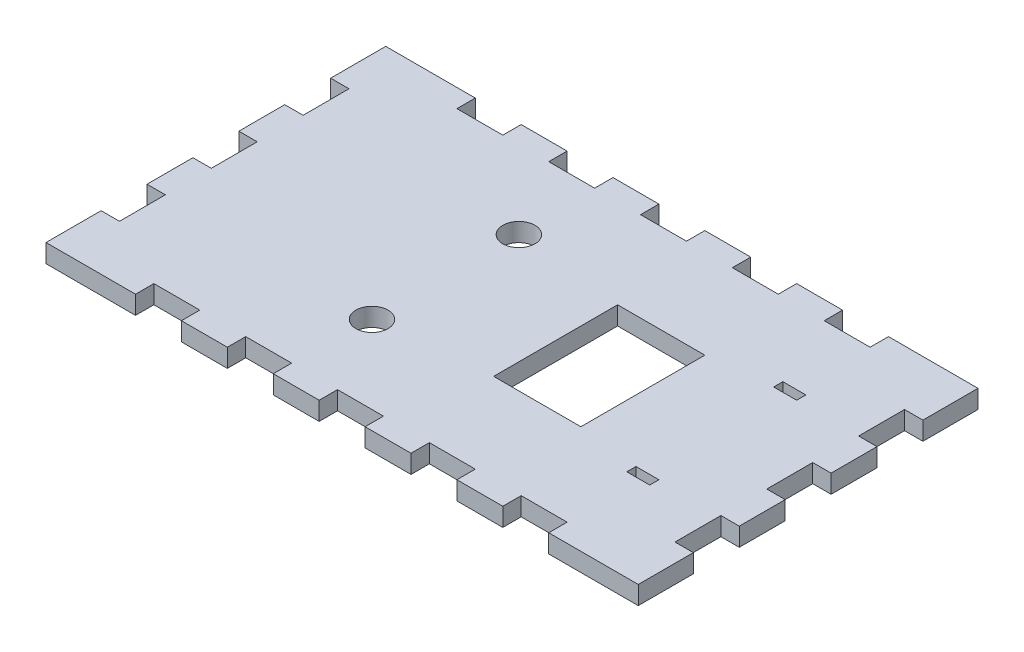
SolidWorks part; units mm, degrees
material "Maple"
ref_plane "Front Plane" through (0, 0, 0) normal (0, 0, 1) x (1, 0, 0)
ref_plane "Top Plane" through (0, 0, 0) normal (0, 1, 0) x (1, 0, 0)
ref_plane "Right Plane" through (0, 0, 0) normal (1, 0, 0) x (0, 0, -1)
sketch "Sketch1" plane through (0, 0, 0) normal (0, 1, 0) x (1, 0, 0)
  line L1 (0, 0) -> (129, 0)
  line L2 (0, 0) -> (0, -74)
  line L3 (0, -74) -> (129, -74)
  line L4 (129, 0) -> (129, -74)
  dimension "D1" = 129
  dimension "D2" = 74
extrude "Boss-Extrude1" add sketch "Sketch1" along normal blind 4
sketch "Sketch2" plane through (0, 4, 0) normal (0, 1, 0) x (1, 0, 0)
  line L0 (0, -37) -> (129, -37) construction
  line L1 (0, 0) -> (0, -74) construction
  line L2 (129, -74) -> (129, 0) construction
  line L3 (50, 0) -> (50, -74) construction
  line L4 (129, 0) -> (0, 0) construction
  line L5 (0, -74) -> (129, -74) construction
  line L7 (74, -23.5) -> (93, -23.5)
  line L8 (74, -23.5) -> (74, -50.5)
  line L9 (74, -50.5) -> (93, -50.5)
  line L10 (93, -23.5) -> (93, -50.5)
  line L11 (74, -23.5) -> (93, -50.5) construction
  line L12 (74, -50.5) -> (93, -23.5) construction
  circle A0 centre (50, -21) radius 3.5
  circle A1 centre (50, -53) radius 3.5
  point P16 (83.5, -37)
  dimension "D1" = 7
  dimension "D2" = 32
  dimension "D3" = 16
  dimension "D4" = 50
  dimension "D5" = 27
  dimension "D6" = 19
  dimension "D7" = 24
extrude "Cut-Extrude1" cut sketch "Sketch2" against normal through all
sketch "Sketch3" plane through (0, 4, 0) normal (0, 1, 0) x (1, 0, 0)
  line L0 (0, -37) -> (129, -37) construction
  line L1 (0, 0) -> (0, -74) construction
  line L2 (129, -74) -> (129, 0) construction
  line L3 (109, 0) -> (109, -74) construction
  line L4 (129, 0) -> (0, 0) construction
  line L5 (0, -74) -> (129, -74) construction
  line L7 (106.5, -20) -> (111.5, -20)
  line L8 (106.5, -20) -> (106.5, -22)
  line L9 (106.5, -22) -> (111.5, -22)
  line L10 (111.5, -20) -> (111.5, -22)
  line L11 (106.5, -20) -> (111.5, -22) construction
  line L12 (106.5, -22) -> (111.5, -20) construction
  line L13 (106.5, -52) -> (111.5, -52)
  line L14 (106.5, -52) -> (106.5, -54)
  line L15 (106.5, -54) -> (111.5, -54)
  line L16 (111.5, -52) -> (111.5, -54)
  line L17 (106.5, -52) -> (111.5, -54) construction
  line L18 (106.5, -54) -> (111.5, -52) construction
  point P12 (109, -21)
  point P17 (109, -53)
  point P22 (109.8837, -64.6218)
  dimension "D3" = 16
  dimension "D1" = 5
  dimension "D2" = 2
  dimension "D4" = 16
  dimension "D5" = 20
extrude "Cut-Extrude2" cut sketch "Sketch3" against normal through all
sketch "Sketch4" plane through (0, 4, 0) normal (0, 1, 0) x (1, 0, 0)
  line L0 (129, -74) -> (129, 0) construction
  line L1 (129, -62) -> (125, -62)
  line L2 (129, -62) -> (129, -52)
  line L3 (129, -52) -> (125, -52)
  line L4 (125, -62) -> (125, -52)
  line L5 (129, -42) -> (125, -42)
  line L6 (129, -42) -> (129, -32)
  line L7 (129, -32) -> (125, -32)
  line L8 (125, -42) -> (125, -32)
  line L9 (0, 0) -> (0, -74) construction
  line L10 (129, -22) -> (125, -22)
  line L11 (129, -22) -> (129, -12)
  line L12 (129, -12) -> (125, -12)
  line L13 (125, -22) -> (125, -12)
  line L14 (0, -62) -> (4, -62)
  line L15 (0, -62) -> (0, -52)
  line L16 (0, -52) -> (4, -52)
  line L17 (4, -62) -> (4, -52)
  line L18 (0, -42) -> (4, -42)
  line L19 (0, -42) -> (0, -32)
  line L20 (0, -32) -> (4, -32)
  line L21 (4, -42) -> (4, -32)
  line L22 (129, 0) -> (0, 0) construction
  line L23 (0, -22) -> (4, -22)
  line L24 (0, -22) -> (0, -12)
  line L25 (0, -12) -> (4, -12)
  line L26 (4, -22) -> (4, -12)
  line L27 (109.5, -4) -> (99.5, -4)
  line L28 (109.5, -4) -> (109.5, 0)
  line L29 (109.5, 0) -> (99.5, 0)
  line L30 (99.5, -4) -> (99.5, 0)
  line L31 (0, -74) -> (129, -74) construction
  line L32 (89.5, -4) -> (79.5, -4)
  line L33 (89.5, -4) -> (89.5, 0)
  line L34 (89.5, 0) -> (79.5, 0)
  line L35 (79.5, -4) -> (79.5, 0)
  line L36 (69.5, -4) -> (59.5, -4)
  line L37 (69.5, -4) -> (69.5, 0)
  line L38 (69.5, 0) -> (59.5, 0)
  line L39 (59.5, -4) -> (59.5, 0)
  line L40 (49.5, -4) -> (39.5, -4)
  line L41 (49.5, -4) -> (49.5, 0)
  line L42 (49.5, 0) -> (39.5, 0)
  line L43 (39.5, -4) -> (39.5, 0)
  line L44 (29.5, -4) -> (19.5, -4)
  line L45 (29.5, -4) -> (29.5, 0)
  line L46 (29.5, 0) -> (19.5, 0)
  line L47 (19.5, -4) -> (19.5, 0)
  line L48 (109.5, -74) -> (99.5, -74)
  line L49 (109.5, -74) -> (109.5, -70)
  line L50 (109.5, -70) -> (99.5, -70)
  line L51 (99.5, -74) -> (99.5, -70)
  line L53 (89.5, -74) -> (79.5, -74)
  line L54 (89.5, -74) -> (89.5, -70)
  line L55 (89.5, -70) -> (79.5, -70)
  line L56 (79.5, -74) -> (79.5, -70)
  line L57 (69.5, -74) -> (59.5, -74)
  line L58 (69.5, -74) -> (69.5, -70)
  line L59 (69.5, -70) -> (59.5, -70)
  line L60 (59.5, -74) -> (59.5, -70)
  line L61 (49.5, -74) -> (39.5, -74)
  line L62 (49.5, -74) -> (49.5, -70)
  line L63 (49.5, -70) -> (39.5, -70)
  line L64 (39.5, -74) -> (39.5, -70)
  line L65 (29.5, -74) -> (19.5, -74)
  line L66 (29.5, -74) -> (29.5, -70)
  line L67 (29.5, -70) -> (19.5, -70)
  line L68 (19.5, -74) -> (19.5, -70)
  point P72 (4, -62)
  point P73 (4, -62)
extrude "Cut-Extrude3" cut sketch "Sketch4" against normal through all
equation "\"D3@Sketch2\"=\"D2@Sketch2\"/2"
equation "\"D4@Sketch3\"=\"D3@Sketch3\""
